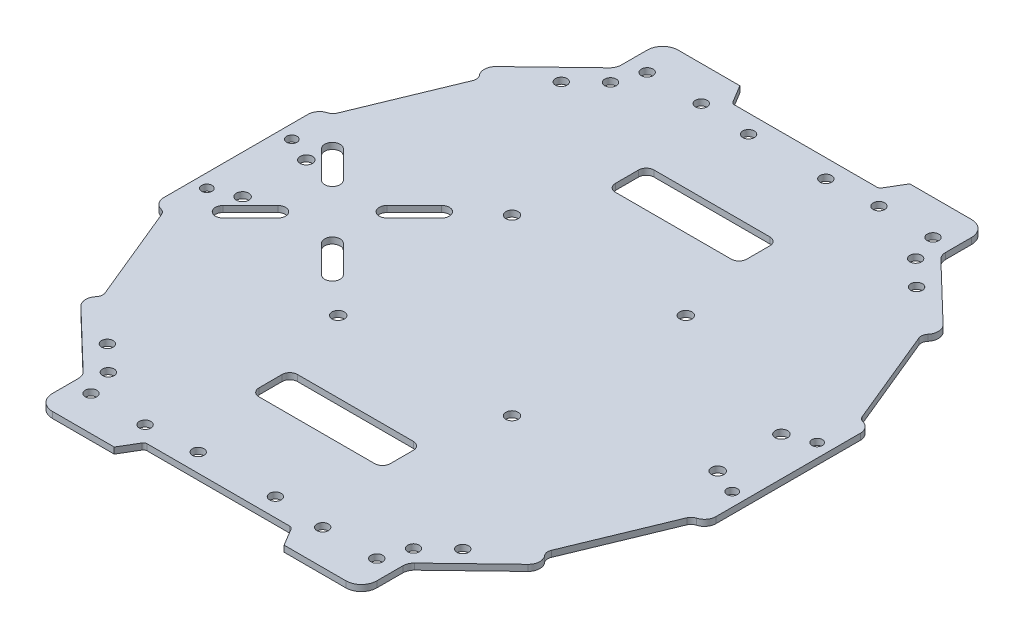
SolidWorks part; units mm, degrees
ref_plane "Front Plane" through (0, 0, 0) normal (0, 0, 1) x (1, 0, 0)
ref_plane "Top Plane" through (0, 0, 0) normal (0, 1, 0) x (1, 0, 0)
ref_plane "Right Plane" through (0, 0, 0) normal (1, 0, 0) x (0, 0, -1)
ref_plane "Plane1"
sketch "Sketch1" plane through (0, 0, 0) normal (0, 1, 0) x (-1, 0, 0)
  line L0 (59.7752, 259.0599) -> (56.7752, 264.0599)
  line L1 (56.7752, 264.0599) -> (36.7752, 264.0599)
  line L2 (36.7752, 264.0599) -> (36.7752, 252.0599)
  line L3 (36.7752, 252.0599) -> (18.7553, 234.7311)
  line L4 (18.7553, 234.7311) -> (21.5279, 231.8479)
  line L5 (21.5279, 231.8479) -> (10.2752, 204.5599)
  line L6 (10.2752, 204.5599) -> (7.2752, 204.5599)
  line L7 (7.2752, 204.5599) -> (7.2752, 183.0599)
  line L8 (7.2752, 183.0599) -> (7.2752, 161.5599)
  line L9 (7.2752, 161.5599) -> (10.2752, 161.5599)
  line L10 (10.2752, 161.5599) -> (21.5279, 134.2718)
  line L11 (21.5279, 134.2718) -> (18.7553, 131.3886)
  line L12 (18.7553, 131.3886) -> (36.7752, 114.0599)
  line L13 (36.7752, 114.0599) -> (36.7752, 102.0599)
  line L14 (36.7752, 102.0599) -> (56.7752, 102.0599)
  line L15 (56.7752, 102.0599) -> (59.7752, 107.0599)
  line L16 (59.7752, 107.0599) -> (78.7752, 107.0599)
  line L17 (78.7752, 107.0599) -> (97.7752, 107.0599)
  line L18 (97.7752, 107.0599) -> (100.7752, 102.0599)
  line L19 (100.7752, 102.0599) -> (120.7752, 102.0599)
  line L20 (120.7752, 102.0599) -> (120.7752, 114.0599)
  line L21 (120.7752, 114.0599) -> (138.795, 131.3886)
  line L22 (138.795, 131.3886) -> (136.0224, 134.2718)
  line L23 (136.0224, 134.2718) -> (147.2752, 161.5599)
  line L24 (147.2752, 161.5599) -> (150.2752, 161.5599)
  line L25 (150.2752, 161.5599) -> (150.2752, 183.0599)
  line L26 (150.2752, 183.0599) -> (150.2752, 204.5599)
  line L27 (150.2752, 204.5599) -> (147.2752, 204.5599)
  line L28 (147.2752, 204.5599) -> (136.0224, 231.8479)
  line L29 (136.0224, 231.8479) -> (138.795, 234.7311)
  line L30 (138.795, 234.7311) -> (120.7752, 252.0599)
  line L31 (120.7752, 252.0599) -> (120.7752, 264.0599)
  line L32 (120.7752, 264.0599) -> (100.7752, 264.0599)
  line L33 (100.7752, 264.0599) -> (97.7752, 259.0599)
  line L34 (97.7752, 259.0599) -> (78.7752, 259.0599)
  line L35 (78.7752, 259.0599) -> (59.7752, 259.0599)
  line L37 (2.8032, 179.0599) -> (-51.2357, 179.0599)
  line L38 (78.7752, 259.0599) -> (78.7752, 107.0599) construction
  line L39 (150.2752, 183.0599) -> (7.2752, 183.0599) construction
  line L40 (2.8032, 179.0599) -> (2.8032, 183.0599)
  line L41 (2.8032, 183.0599) -> (-51.2357, 183.0599)
  line L42 (-51.2357, 179.0599) -> (-51.2357, 183.0599)
  line L43 (2.8032, 179.0599) -> (-51.2357, 183.0599) construction
  line L44 (2.8032, 183.0599) -> (-51.2357, 179.0599) construction
  line L85 (91.8838, 199.6325) -> (91.9874, 199.5289)
  line L87 (95.3777, 196.1387) -> (95.4193, 196.097)
  circle A0 centre (55.7752, 111.0599) radius 1.5
  circle A1 centre (39.2752, 118.0599) radius 1.5
  circle A4 centre (17.2752, 174.8099) radius 1.6
  circle A10 centre (101.2752, 205.5599) radius 1.6
  circle A11 centre (56.2752, 205.5599) radius 1.6
  circle A12 centre (56.2752, 160.5599) radius 1.6
  circle A13 centre (101.2752, 160.5599) radius 1.6
  circle A22 centre (41.7752, 255.0599) radius 1.5
  circle A23 centre (39.2752, 248.0599) radius 1.5
  circle A24 centre (10.7752, 194.0599) radius 1.35
  circle A25 centre (88.7752, 111.8099) radius 1.5
  circle A27 centre (115.7752, 111.0599) radius 1.5
  circle A28 centre (118.2752, 118.0599) radius 1.5
  circle A29 centre (140.2752, 174.8099) radius 1.6
  circle A30 centre (115.7752, 255.0599) radius 1.5
  circle A31 centre (88.7752, 254.3099) radius 1.5
  circle A32 centre (140.2752, 191.3099) radius 1.6
  circle A33 centre (146.7752, 194.0599) radius 1.35
  circle A53 centre (101.7752, 255.0599) radius 1.5
  circle A54 centre (118.2752, 248.0599) radius 1.5
  circle A55 centre (146.7752, 172.0599) radius 1.35
  circle A57 centre (101.7752, 111.0599) radius 1.5
  circle A69 centre (17.2752, 191.3099) radius 1.6
  circle A71 centre (55.7752, 255.0599) radius 1.5
  circle A73 centre (68.7752, 254.3099) radius 1.5
  circle A74 centre (10.7752, 172.0599) radius 1.35
  circle A76 centre (68.7752, 111.8099) radius 1.5
  circle A77 centre (41.7752, 111.0599) radius 1.5
  circle A82 centre (32.7752, 124.3099) radius 1.5
  circle A86 centre (124.7752, 241.8099) radius 1.5
  circle A87 centre (32.7752, 241.8099) radius 1.5
  circle A91 centre (124.7752, 124.3099) radius 1.5
  point P40 (-24.2162, 181.0599)
  point P41 (150.2752, 193.8099)
  dimension "D1" = 143
  dimension "D2" = 162
  dimension "D3" = 22.5
  dimension "D4" = 22.5
extrude "Extrusion1" add sketch "Sketch1" along normal blind 1.6
fillet "Fillet1" radius 1 4 edges at (-97.7752, 0.8, 107.0599) (-59.7752, 0.8, 107.0599) (-59.7752, 0.8, 259.0599) (-97.7752, 0.8, 259.0599)
fillet "Fillet2" radius 4 4 edges at (-120.7752, 0.8, 102.0599) (-36.7752, 0.8, 102.0599) (-120.7752, 0.8, 264.0599) (-36.7752, 0.8, 264.0599)
fillet "Fillet3" radius 3 4 edges at (-120.7752, 0.8, 114.0599) (-36.7752, 0.8, 114.0599) (-36.7752, 0.8, 252.0599) (-120.7752, 0.8, 252.0599)
fillet "Fillet4" radius 3 1 edges at (-138.795, 0.8, 234.7311)
fillet "Fillet5" radius 2 1 edges at (-136.0224, 0.8, 231.8479)
fillet "Fillet6" radius 2 1 edges at (-21.5279, 0.8, 231.8479)
fillet "Fillet7" radius 3 1 edges at (-18.7553, 0.8, 234.7311)
fillet "Fillet8" radius 3 2 edges at (-138.795, 0.8, 131.3886) (-18.7553, 0.8, 131.3886)
fillet "Fillet9" radius 2 2 edges at (-21.5279, 0.8, 134.2718) (-136.0224, 0.8, 134.2718)
fillet "Fillet10" radius 2 4 edges at (-10.2752, 0.8, 161.5599) (-10.2752, 0.8, 204.5599) (-147.2752, 0.8, 204.5599) (-147.2752, 0.8, 161.5599)
fillet "Fillet11" radius 3 4 edges at (-150.2752, 0.8, 161.5599) (-150.2752, 0.8, 204.5599) (-7.2752, 0.8, 204.5599) (-7.2752, 0.8, 161.5599)
sketch "Sketch2" plane through (0, 1.6, 0) normal (0, 1, 0) x (1, 0, 0)
  line L0 (-60.3413, -107.0599) -> (-97.209, -107.0599) construction
  line L1 (-93.0095, -132.0599) -> (-63.0095, -132.0599)
  line L2 (-95.0095, -134.0599) -> (-95.0095, -140.0599)
  line L3 (-93.0095, -142.0599) -> (-63.0095, -142.0599)
  line L4 (-61.0095, -134.0599) -> (-61.0095, -140.0599)
  line L5 (-95.0095, -132.0599) -> (-61.0095, -142.0599) construction
  line L6 (-95.0095, -142.0599) -> (-61.0095, -132.0599) construction
  line L7 (-93.3036, -224.0599) -> (-63.3036, -224.0599)
  line L8 (-95.3036, -226.0599) -> (-95.3036, -232.0599)
  line L9 (-93.3036, -234.0599) -> (-63.3036, -234.0599)
  line L10 (-61.3036, -226.0599) -> (-61.3036, -232.0599)
  line L11 (-95.3036, -224.0599) -> (-61.3036, -234.0599) construction
  line L12 (-95.3036, -234.0599) -> (-61.3036, -224.0599) construction
  line L14 (-97.209, -259.0599) -> (-60.3413, -259.0599) construction
  arc A0 (-95.3036, -226.0599) -> (-93.3036, -224.0599) centre (-93.3036, -226.0599) cw
  arc A1 (-95.3036, -232.0599) -> (-93.3036, -234.0599) centre (-93.3036, -232.0599) ccw
  arc A2 (-63.3036, -234.0599) -> (-61.3036, -232.0599) centre (-63.3036, -232.0599) ccw
  arc A3 (-63.3036, -224.0599) -> (-61.3036, -226.0599) centre (-63.3036, -226.0599) cw
  arc A4 (-61.0095, -134.0599) -> (-63.0095, -132.0599) centre (-63.0095, -134.0599) ccw
  arc A5 (-61.0095, -140.0599) -> (-63.0095, -142.0599) centre (-63.0095, -140.0599) cw
  arc A6 (-95.0095, -140.0599) -> (-93.0095, -142.0599) centre (-93.0095, -140.0599) ccw
  arc A7 (-95.0095, -134.0599) -> (-93.0095, -132.0599) centre (-93.0095, -134.0599) cw
  point P0 (-78.0095, -137.0599)
  point P6 (-78.3036, -229.0599)
  dimension "D3" = 2
  dimension "D1" = 30
  dimension "D2" = 30
extrude "Cut-Extrude1" cut sketch "Sketch2" against normal blind 10 contours L2 A6 L3 A5 L4 A4 L1 A7 | L8 A1 L9 A2 L10 A3 L7 A0
sketch "Sketch3" plane through (0, 1.6, 0) normal (0, 1, 0) x (1, 0, 0)
  line L0 (-118.2041, -175.9888) -> (-111.133, -168.9177) construction
  line L3 (-116.7752, -264.0599) -> (-100.7752, -264.0599) construction
  line L4 (-119.6183, -174.5746) -> (-112.5472, -167.5035)
  line L7 (-143.3987, -164.9363) -> (-107.1516, -201.1834) construction
  line L8 (-116.7899, -177.403) -> (-109.7188, -170.332)
  line L11 (-139.4173, -197.202) -> (-132.3462, -190.1309) construction
  line L14 (-140.8315, -195.7878) -> (-133.7604, -188.7167)
  line L15 (-142.9283, -200.713) -> (-111.3473, -169.132) construction
  line L16 (-138.0031, -198.6162) -> (-130.932, -191.5452)
  line L17 (-139.4173, -168.9177) -> (-132.3462, -175.9888) construction
  line L18 (-138.0031, -167.5035) -> (-130.932, -174.5746)
  line L19 (-140.8315, -170.332) -> (-133.7604, -177.403)
  line L20 (-118.2041, -190.1309) -> (-111.133, -197.202) construction
  line L21 (-116.7899, -188.7167) -> (-109.7188, -195.7878)
  line L22 (-119.6183, -191.5452) -> (-112.5472, -198.6162)
  line L23 (-150.2752, -164.3774) -> (-150.2752, -201.7424) construction
  arc A8 (-119.6183, -174.5746) -> (-116.7899, -177.403) centre (-118.2041, -175.9888) ccw
  arc A9 (-109.7188, -170.332) -> (-112.5472, -167.5035) centre (-111.133, -168.9177) ccw
  arc A10 (-140.8315, -195.7878) -> (-138.0031, -198.6162) centre (-139.4173, -197.202) ccw
  arc A11 (-130.932, -191.5452) -> (-133.7604, -188.7167) centre (-132.3462, -190.1309) ccw
  arc A12 (-138.0031, -167.5035) -> (-140.8315, -170.332) centre (-139.4173, -168.9177) ccw
  arc A13 (-133.7604, -177.403) -> (-130.932, -174.5746) centre (-132.3462, -175.9888) ccw
  arc A14 (-116.7899, -188.7167) -> (-119.6183, -191.5452) centre (-118.2041, -190.1309) ccw
  arc A15 (-112.5472, -198.6162) -> (-109.7188, -195.7878) centre (-111.133, -197.202) ccw
  point P2 (-114.6686, -172.4533)
  point P7 (-135.8818, -193.6665)
  point P14 (-135.8818, -172.4533)
  point P23 (-114.6686, -193.6665)
  point P32 (-150.2752, -183.0599)
  point P33 (-134.5257, -192.3104)
  point P36 (-125.2752, -183.0599)
  point P37 (-134.5257, -192.3104)
  point P38 (-131.844, -176.4911)
  point P39 (0, 0)
  point P40 (-133.2935, -191.0782)
  dimension "D3" = 15
  dimension "D5" = 15
  dimension "D2" = 15
  dimension "D1" = 25
  dimension "D4" = 15
  dimension "D6" = 81
extrude "Cut-Extrude2" cut sketch "Sketch3" against normal blind 10
